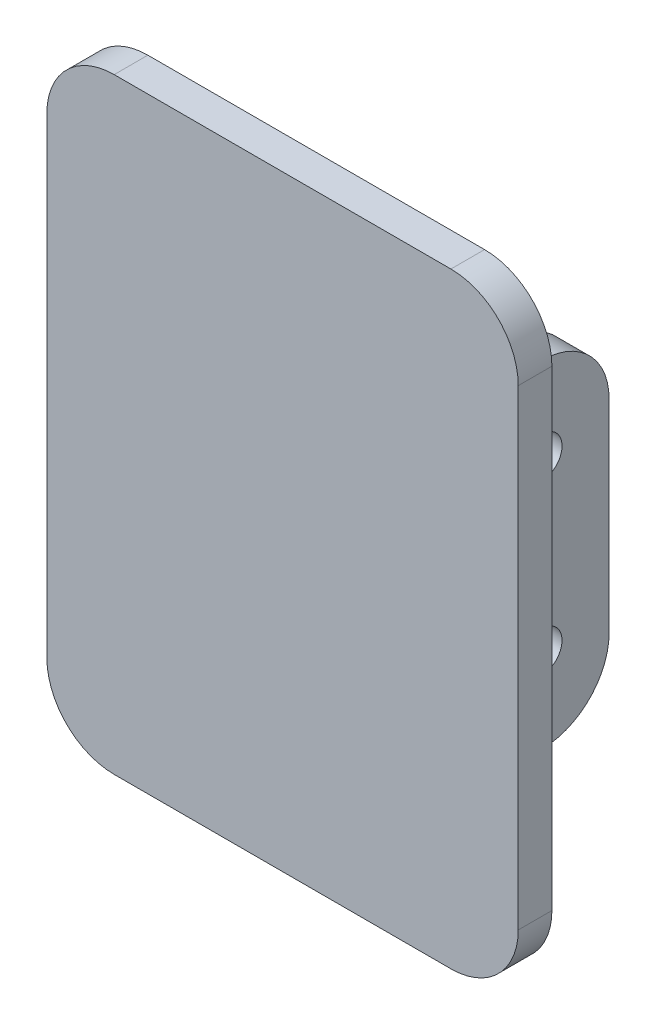
SolidWorks part; units mm, degrees
material "6061-T6 (SS)"
ref_plane "Front Plane" through (0, 0, 0) normal (0, 0, 1) x (1, 0, 0)
ref_plane "Top Plane" through (0, 0, 0) normal (0, 1, 0) x (1, 0, 0)
ref_plane "Right Plane" through (0, 0, 0) normal (1, 0, 0) x (0, 0, -1)
sketch "Sketch1" plane through (0, 0, 0) normal (0, 0, 1) x (1, 0, 0)
  line L1 (-35, 45) -> (35, 45)
  line L2 (-35, 45) -> (-35, -45)
  line L3 (-35, -45) -> (35, -45)
  line L4 (35, 45) -> (35, -45)
  line L5 (-35, 45) -> (35, -45) construction
  line L6 (-35, -45) -> (35, 45) construction
  point P0 (0, 0)
  dimension "D1" = 70
  dimension "D2" = 90
extrude "Boss-Extrude1" add sketch "Sketch1" along normal blind 5
sketch "Sketch3" plane through (0, 0, 0) normal (0, 0, -1) x (-1, 0, 0)
  line L0 (-11, 36.7243) -> (-11, -38.6187) construction
  line L1 (1.5, -25) -> (-3.5, -25)
  line L2 (-23.5, 25) -> (-18.5, 25)
  line L3 (-23.5, 25) -> (-23.5, -25)
  line L4 (-23.5, -25) -> (-18.5, -25)
  line L5 (-18.5, 25) -> (-18.5, -25)
  line L6 (-23.5, 25) -> (-18.5, -25) construction
  line L7 (-23.5, -25) -> (-18.5, 25) construction
  line L8 (1.5, 25) -> (1.5, -25)
  line L9 (1.5, 25) -> (-3.5, 25)
  line L10 (-3.5, 25) -> (-3.5, -25)
  line L11 (-35, -45) -> (-35, 45) construction
  point P3 (-21, 0)
  dimension "D1" = 5
  dimension "D2" = 50
  dimension "D3" = 10
  dimension "D4" = 24
extrude "Boss-Extrude2" add sketch "Sketch3" along normal blind 20
sketch "Sketch4" plane through (23.5, 0, 0) normal (1, 0, 0) x (0, 0, -1)
  line L0 (-18.5307, 0) -> (40.1987, 0) construction
  line L1 (20, 25) -> (20, -25) construction
  circle A0 centre (10, 12.5) radius 3
  circle A1 centre (10, -12.5) radius 3
  dimension "D3" = 6
  dimension "D1" = 12.5
  dimension "D2" = 10
extrude "Cut-Extrude1" cut sketch "Sketch4" against normal through all
fillet "Fillet1" radius 3 6 edges at (1, 25, 0) (-1.5, 0, 0) (1, -25, 0) (21, -25, 0) (21, 25, 0) (23.5, 0, 0)
fillet "Fillet2" radius 10 4 edges at (1, 25, -20) (1, -25, -20) (21, -25, -20) (21, 25, -20)
fillet "Fillet3" radius 10 4 edges at (-35, -45, 2.5) (35, -45, 2.5) (35, 45, 2.5) (-35, 45, 2.5)
